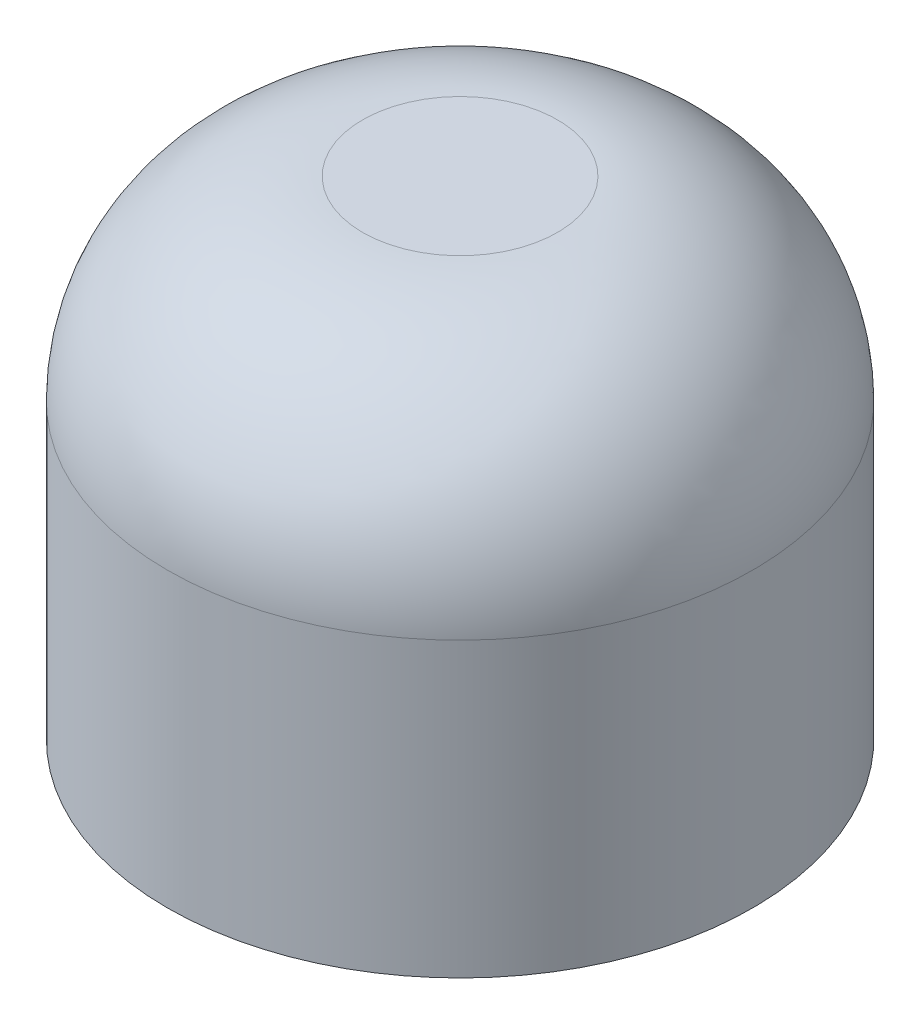
SolidWorks part; units mm, degrees
material "PET"
ref_plane "Спереди" through (0, 0, 0) normal (0, 0, 1) x (1, 0, 0)
ref_plane "Сверху" through (0, 0, 0) normal (0, 1, 0) x (1, 0, 0)
ref_plane "Справа" through (0, 0, 0) normal (1, 0, 0) x (0, 0, -1)
other "Configuration Table"
sketch "Эскиз1" plane through (0, 0, 0) normal (0, 1, 0) x (1, 0, 0)
  circle A0 centre (0, 0) radius 3
extrude "Бобышка-Вытянуть1" add sketch "Эскиз1" along normal blind 5
fillet "Скругление2" radius 2 1 edges at (0, 5, 3)
